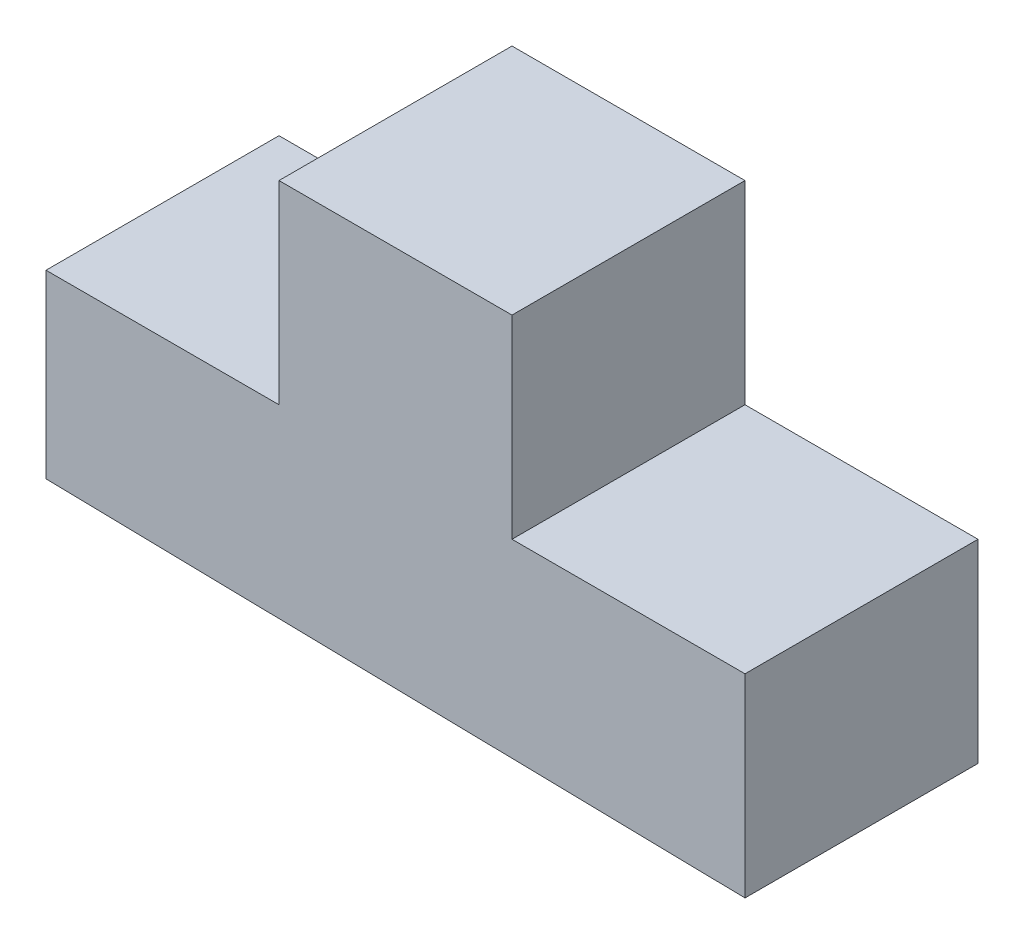
SolidWorks part; units mm, degrees
ref_plane "Front Plane" through (0, 0, 0) normal (0, 0, 1) x (1, 0, 0)
ref_plane "Top Plane" through (0, 0, 0) normal (0, 1, 0) x (1, 0, 0)
ref_plane "Right Plane" through (0, 0, 0) normal (1, 0, 0) x (0, 0, -1)
sketch "Sketch1" plane through (0, 0, 0) normal (0, 0, 1) x (1, 0, 0)
  line L0 (0, 0) -> (90, -1.7307)
  line L1 (90, -1.7307) -> (90, 23.2693)
  line L2 (0, 0) -> (0, 23.2693)
  line L3 (0, 23.2693) -> (30, 23.2693)
  line L4 (90, 23.2693) -> (60, 23.2693)
  line L5 (30, 23.2693) -> (30, 48.2693)
  line L6 (60, 23.2693) -> (60, 48.2693)
  line L7 (30, 48.2693) -> (60, 48.2693)
  dimension "D1" = 90
  dimension "D2" = 25
  dimension "D3" = 25
  dimension "D4" = 30
  dimension "D5" = 30
extrude "Boss-Extrude1" add sketch "Sketch1" along normal blind 30
